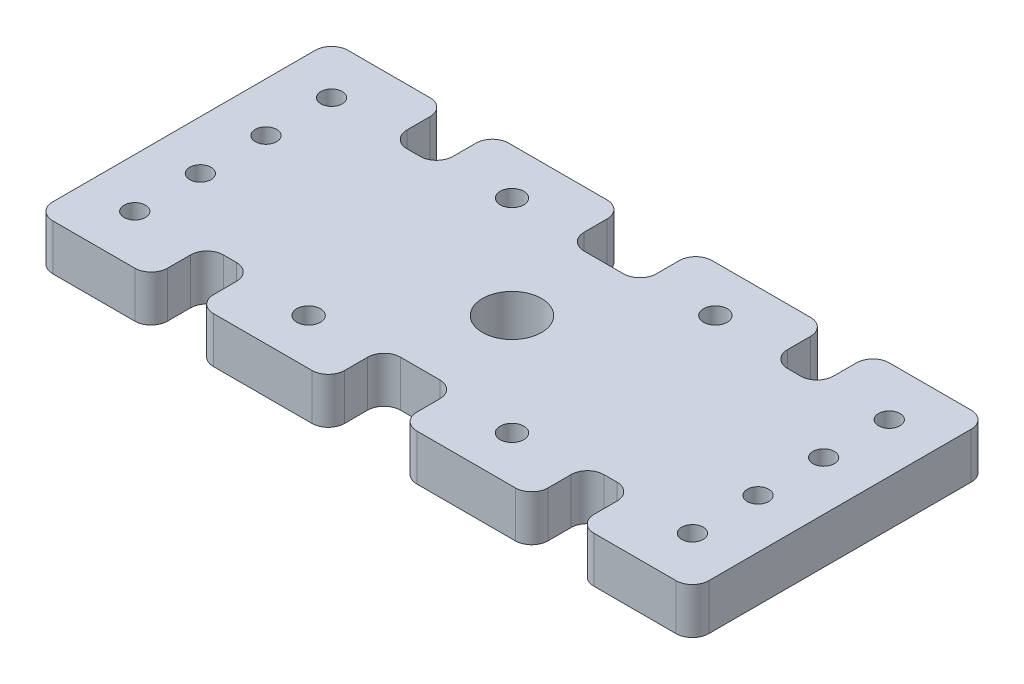
SolidWorks part; units mm, degrees
ref_plane "Front Plane" through (0, 0, 0) normal (0, 0, 1) x (1, 0, 0)
ref_plane "Top Plane" through (0, 0, 0) normal (0, 1, 0) x (1, 0, 0)
ref_plane "Right Plane" through (0, 0, 0) normal (1, 0, 0) x (0, 0, -1)
sketch "Sketch1" plane through (0, 0, 0) normal (0, 1, 0) x (1, 0, 0)
  line L0 (-15.5, -15.5) -> (-15.5, 15.5) construction
  line L1 (50, 22.5) -> (-50, 22.5)
  line L2 (50, 22.5) -> (50, -22.5)
  line L3 (50, -22.5) -> (-50, -22.5)
  line L4 (-50, 22.5) -> (-50, -22.5)
  line L5 (50, 22.5) -> (-50, -22.5) construction
  line L6 (50, -22.5) -> (-50, 22.5) construction
  line L7 (15.5, 15.5) -> (-15.5, 15.5) construction
  point P0 (0, 0)
  point P5 (-15.5, 15.5)
  point P6 (15.5, 15.5)
  point P8 (-15.5, -15.5)
  point P9 (15.5, -15.5)
  point P12 (0, 15.5)
  point P14 (-15.5, 0)
  dimension "D3" = 31
  dimension "D1" = 100
  dimension "D2" = 45
extrude "Boss-Extrude1" add sketch "Sketch1" along normal blind 7
hole_wizard "M3 Clearance Hole1" positions "Sketch2" profile "Sketch3" hole size "M3" standard "ANSI Metric" end condition through all
sketch "Sketch2" plane through (0, 7, 0) normal (0, 1, 0) x (1, 0, 0)
  point P1 (15.5, 15.5)
  point P3 (-15.5, 15.5)
  point P5 (-15.5, -15.5)
  point P7 (15.5, -15.5)
sketch "Sketch3" plane through (15.5, 7, -15.5) normal (1, 0, 0) x (0, 0, 1)
  line L0 (0, 0) -> (0, 7)
  line L1 (0, 7) -> (1.8, 7)
  line L2 (1.8, 7) -> (1.8, 0)
  line L5 (1.8, 0) -> (0, 0)
  line L11 (0, -6.35) -> (0, 107.95) construction
  dimension "Thru Hole Dia." = 3.6
  dimension "Thru Hole Depth" = 7
hole_wizard "M8 Clearance Hole1" positions "Sketch4" profile "Sketch5" hole size "M8" standard "ANSI Metric" end condition through all
sketch "Sketch4" plane through (0, 7, 0) normal (0, 1, 0) x (1, 0, 0)
  point P1 (0, 0)
sketch "Sketch5" plane through (0, 7, 0) normal (1, 0, 0) x (0, 0, 1)
  line L0 (0, 0) -> (0, 7)
  line L1 (0, 7) -> (4.5, 7)
  line L2 (4.5, 7) -> (4.5, 0)
  line L5 (4.5, 0) -> (0, 0)
  line L11 (0, -6.35) -> (0, 107.95) construction
  dimension "Thru Hole Dia." = 9
  dimension "Thru Hole Depth" = 7
sketch "Sketch6" plane through (0, 7, 0) normal (0, 1, 0) x (1, 0, 0)
  line L0 (50, 22.5) -> (-50, 22.5) construction
  line L1 (-50, 22.5) -> (-50, -22.5) construction
  point P0 (-42.5, 15)
  dimension "D1" = 7.5
  dimension "D2" = 7.5
hole_wizard "#4 Clearance Hole1" positions "Sketch7" profile "Sketch8" hole size "#4" standard "ANSI Inch" end condition through all
sketch "Sketch7" plane through (0, 7, 0) normal (0, 1, 0) x (1, 0, 0)
  point P0 (-42.5, 15)
sketch "Sketch8" plane through (-42.5, 7, -15) normal (1, 0, 0) x (0, 0, 1)
  line L0 (0, 0) -> (0, 7)
  line L1 (0, 7) -> (1.6319, 7)
  line L2 (1.6319, 7) -> (1.6319, 0)
  line L5 (1.6319, 0) -> (0, 0)
  line L11 (0, -6.35) -> (0, 107.95) construction
  dimension "Thru Hole Dia." = 3.2639
  dimension "Thru Hole Depth" = 7
pattern_linear "LPattern1" count 4 spacing 10 along (0, 0, 1) of "#4 Clearance Hole1"
mirror "Mirror1" about plane through (0, 0, 0) normal (1, 0, 0) of "LPattern1", "#4 Clearance Hole1"
sketch "Sketch9" plane through (0, 7, 0) normal (0, 1, 0) x (1, 0, 0)
  line L0 (-32.5, 22.5) -> (-32.5, 14)
  line L1 (50, 22.5) -> (-50, 22.5) construction
  line L2 (-32.5, 14) -> (-25.5, 14)
  line L3 (-25.5, 14) -> (-25.5, 22.5)
  line L4 (-32.5, -22.5) -> (-32.5, -14)
  line L5 (-50, -22.5) -> (50, -22.5) construction
  line L6 (-32.5, -14) -> (-25.5, -14)
  line L7 (-25.5, -14) -> (-25.5, -22.5)
  line L8 (25.5, -22.5) -> (25.5, -14)
  line L9 (25.5, -14) -> (32.5, -14)
  line L10 (32.5, -14) -> (32.5, -22.5)
  line L11 (25.5, 22.5) -> (25.5, 14)
  line L12 (25.5, 14) -> (32.5, 14)
  line L13 (32.5, 14) -> (32.5, 22.5)
  line L14 (-5.5, 22.5) -> (-5.5, 14)
  line L15 (-5.5, 14) -> (5.5, 14)
  line L16 (5.5, 14) -> (5.5, 22.5)
  line L17 (-5.5, -22.5) -> (-5.5, -14)
  line L18 (-5.5, -14) -> (5.5, -14)
  line L19 (5.5, -14) -> (5.5, -22.5)
  line L20 (-32.5, 22.5) -> (-25.5, 22.5)
  line L21 (-5.5, 22.5) -> (5.5, 22.5)
  line L22 (25.5, 22.5) -> (32.5, 22.5)
  line L23 (-32.5, -22.5) -> (-25.5, -22.5)
  line L24 (-5.5, -22.5) -> (5.5, -22.5)
  line L25 (25.5, -22.5) -> (32.5, -22.5)
  point P26 (-42.5, 15)
  point P27 (-15.5, 15.5)
  point P28 (15.5, 15.5)
  point P33 (42.5, 15)
  dimension "D1" = 10
  dimension "D2" = 10
  dimension "D3" = 10
  dimension "D4" = 10
  dimension "D5" = 10
  dimension "D6" = 10
  dimension "D7" = 8.5
extrude "Cut-Extrude1" cut sketch "Sketch9" against normal through all
fillet "Fillet1" radius 2.5 28 edges at (-32.5, 3.5, 22.5) (-32.5, 3.5, 14) (-25.5, 3.5, 14) (-25.5, 3.5, 22.5) (-5.5, 3.5, 22.5) (-5.5, 3.5, 14) (5.5, 3.5, 14) (5.5, 3.5, 22.5) (25.5, 3.5, 22.5) (32.5, 3.5, 22.5) (50, 3.5, 22.5) (50, 3.5, -22.5) (32.5, 3.5, -22.5) (32.5, 3.5, -14) (25.5, 3.5, -14) (25.5, 3.5, -22.5) (5.5, 3.5, -22.5) (5.5, 3.5, -14) (-5.5, 3.5, -14) (-5.5, 3.5, -22.5) (-25.5, 3.5, -22.5) (-25.5, 3.5, -14) (-32.5, 3.5, -14) (-32.5, 3.5, -22.5) (-50, 3.5, -22.5) (-50, 3.5, 22.5) (32.5, 3.5, 14) (25.5, 3.5, 14)
